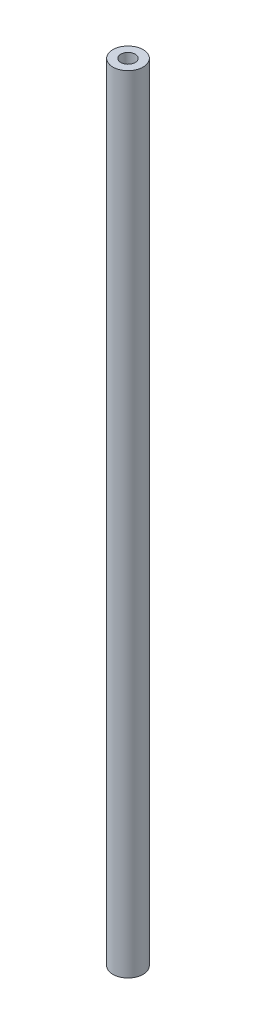
SolidWorks part; units mm, degrees
material "6061 Alloy"
ref_plane "Front Plane" through (0, 0, 0) normal (0, 0, 1) x (1, 0, 0)
ref_plane "Top Plane" through (0, 0, 0) normal (0, 1, 0) x (1, 0, 0)
ref_plane "Right Plane" through (0, 0, 0) normal (1, 0, 0) x (0, 0, -1)
sketch "Sketch1" plane through (0, 0, 0) normal (0, 1, 0) x (1, 0, 0)
  circle A0 centre (0, 0) radius 3.175
  circle A1 centre (0, 0) radius 1.524
  dimension "D1" = 6.35
  dimension "D2" = 3.048
extrude "Boss-Extrude1" add sketch "Sketch1" along normal blind 165.1
